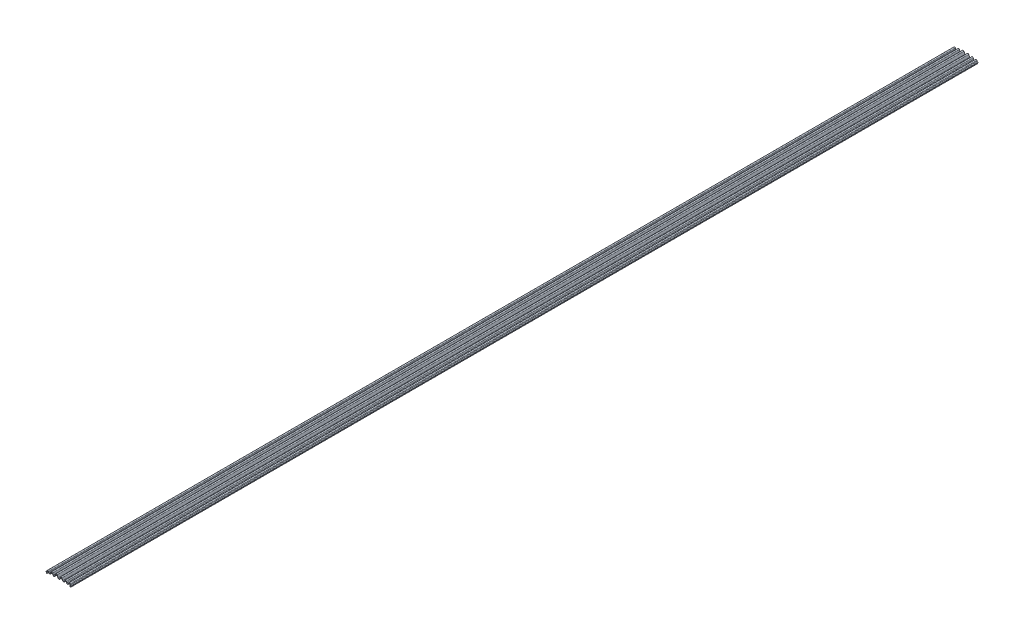
SolidWorks part; units mm, degrees
material "6463-T6"
ref_plane "Front Plane" through (0, 0, 0) normal (0, 0, 1) x (1, 0, 0)
ref_plane "Top Plane" through (0, 0, 0) normal (0, 1, 0) x (1, 0, 0)
ref_plane "Right Plane" through (0, 0, 0) normal (1, 0, 0) x (0, 0, -1)
sketch "Sketch1" plane through (0, 0, 0) normal (0, 0, 1) x (1, 0, 0)
  line L0 (-50.7848, 0.5715) -> (-50.5597, -0.0467)
  line L1 (-47.9908, -0.381) -> (-50.0824, -0.381)
  line L4 (-47.9908, -2.794) -> (-49.0157, -2.794)
  line L5 (-49.3737, -3.3053) -> (-49.1473, -3.9275)
  line L6 (-52.094, 1.3335) -> (52.094, 1.3335) construction
  line L7 (0, 14.1993) -> (0, -14.1993) construction
  line L9 (49.3737, -3.3053) -> (49.1473, -3.9275)
  line L10 (-50.7848, 1.3335) -> (-50.7848, 0.5715)
  line L12 (47.9908, -2.794) -> (49.0157, -2.794)
  line L14 (47.9908, -0.381) -> (50.0976, -0.381)
  line L15 (50.8, 0.5715) -> (50.575, -0.0467)
  line L20 (-46.5413, 2.5226) -> (-45.1353, 5.5376)
  line L21 (-41.6581, 5.5376) -> (-40.2522, 2.5226)
  line L22 (-31.7347, 2.5226) -> (-29.16, 8.0441)
  line L23 (-25.6828, 8.0441) -> (-23.1081, 2.5226)
  line L24 (-14.5906, 2.5226) -> (-10.6158, 11.0468)
  line L25 (-7.1385, 11.0468) -> (-3.1637, 2.5226)
  line L26 (5.3538, 2.5226) -> (8.8101, 9.9345)
  line L27 (12.2873, 9.9345) -> (15.7435, 2.5226)
  line L28 (24.261, 2.5226) -> (26.3257, 6.9503)
  line L29 (29.8029, 6.9503) -> (31.8675, 2.5226)
  line L30 (40.385, 2.5226) -> (41.6686, 5.2752)
  line L31 (45.1458, 5.2752) -> (46.382, 2.6241)
  line L33 (47.7632, 3.2681) -> (46.527, 5.9192)
  line L34 (40.2874, 5.9192) -> (39.0038, 3.1667)
  line L35 (33.2488, 3.1667) -> (31.1841, 7.5943)
  line L36 (24.9444, 7.5943) -> (22.8798, 3.1667)
  line L37 (17.1247, 3.1667) -> (13.6685, 10.5786)
  line L38 (7.4288, 10.5786) -> (3.9726, 3.1667)
  line L39 (-1.7824, 3.1667) -> (-5.7573, 11.6908)
  line L40 (-11.997, 11.6908) -> (-15.9719, 3.1667)
  line L41 (-21.7269, 3.1667) -> (-24.3016, 8.6881)
  line L42 (-30.5413, 8.6881) -> (-33.1159, 3.1667)
  line L43 (-38.871, 3.1667) -> (-40.2769, 6.1817)
  line L44 (-46.5226, 6.1686) -> (-47.9017, 3.1787)
  line L45 (50.8, 0.5715) -> (50.8, 1.3335)
  arc A0 (-47.9908, -2.794) -> (-47.9908, -0.381) centre (-47.9908, -1.5875) ccw
  arc A1 (-48.9187, -4.1555) -> (-46.9934, 0.9543) centre (-47.9908, -1.5875) ccw
  arc A2 (-48.9187, -4.1555) -> (-49.1473, -3.9275) centre (-48.7892, -3.7972) cw
  arc A3 (-49.0157, -2.794) -> (-49.3737, -3.3053) centre (-49.0157, -3.175) ccw
  arc A6 (49.0157, -2.794) -> (49.3737, -3.3053) centre (49.0157, -3.175) cw
  arc A7 (48.9187, -4.1555) -> (49.1473, -3.9275) centre (48.7892, -3.7972) ccw
  arc A8 (48.9187, -4.1555) -> (46.9391, 0.9324) centre (47.9908, -1.5875) cw
  arc A9 (47.9908, -2.794) -> (47.9908, -0.381) centre (47.9908, -1.5875) cw
  arc A12 (-47.1501, 1.5489) -> (-46.5413, 2.5226) centre (-50.8, 4.5085) ccw
  arc A13 (-41.6581, 5.5376) -> (-45.1353, 5.5376) centre (-43.3967, 4.7269) ccw
  arc A14 (-40.2522, 2.5226) -> (-31.7347, 2.5226) centre (-35.9935, 4.5085) ccw
  arc A15 (-25.6828, 8.0441) -> (-29.16, 8.0441) centre (-27.4214, 7.2333) ccw
  arc A16 (-23.1081, 2.5226) -> (-14.5906, 2.5226) centre (-18.8494, 4.5085) ccw
  arc A17 (-7.1385, 11.0468) -> (-10.6158, 11.0468) centre (-8.8771, 10.236) ccw
  arc A18 (-3.1637, 2.5226) -> (5.3538, 2.5226) centre (1.0951, 4.5085) ccw
  arc A19 (12.2873, 9.9345) -> (8.8101, 9.9345) centre (10.5487, 9.1238) ccw
  arc A20 (15.7435, 2.5226) -> (24.261, 2.5226) centre (20.0023, 4.5085) ccw
  arc A21 (29.8029, 6.9503) -> (26.3257, 6.9503) centre (28.0643, 6.1395) ccw
  arc A22 (31.8675, 2.5226) -> (40.385, 2.5226) centre (36.1263, 4.5085) ccw
  arc A23 (45.1458, 5.2752) -> (41.6686, 5.2752) centre (43.4072, 4.4644) ccw
  arc A24 (46.382, 2.6241) -> (47.0829, 1.5305) centre (50.8, 4.6842) ccw
  arc A25 (47.7632, 3.2681) -> (50.8, 1.3335) centre (50.8, 4.6842) ccw
  arc A26 (46.527, 5.9192) -> (40.2874, 5.9192) centre (43.4072, 4.4644) ccw
  arc A27 (33.2488, 3.1667) -> (39.0038, 3.1667) centre (36.1263, 4.5085) ccw
  arc A28 (31.1841, 7.5943) -> (24.9444, 7.5943) centre (28.0643, 6.1395) ccw
  arc A29 (17.1247, 3.1667) -> (22.8798, 3.1667) centre (20.0023, 4.5085) ccw
  arc A30 (13.6685, 10.5786) -> (7.4288, 10.5786) centre (10.5487, 9.1238) ccw
  arc A31 (-1.7824, 3.1667) -> (3.9726, 3.1667) centre (1.0951, 4.5085) ccw
  arc A32 (-5.7573, 11.6908) -> (-11.997, 11.6908) centre (-8.8771, 10.236) ccw
  arc A33 (-21.7269, 3.1667) -> (-15.9719, 3.1667) centre (-18.8494, 4.5085) ccw
  arc A34 (-24.3016, 8.6881) -> (-30.5413, 8.6881) centre (-27.4214, 7.2333) ccw
  arc A35 (-38.871, 3.1667) -> (-33.1159, 3.1667) centre (-35.9935, 4.5085) ccw
  arc A36 (-40.2769, 6.1817) -> (-46.5226, 6.1686) centre (-43.3967, 4.7269) ccw
  arc A37 (-50.7848, 1.3335) -> (-47.9017, 3.1787) centre (-50.7848, 4.5085) ccw
  arc A38 (-46.9934, 0.9543) -> (-47.1501, 1.5489) centre (-46.8542, 1.309) cw
  arc A39 (-50.0824, -0.381) -> (-50.5597, -0.0467) centre (-50.0824, 0.127) cw
  arc A40 (50.575, -0.0467) -> (50.0976, -0.381) centre (50.0976, 0.127) cw
  arc A41 (46.9391, 0.9324) -> (47.0829, 1.5305) centre (46.7924, 1.284) ccw
  point P2 (0, 1.3335)
  point P34 (49.5751, -3.3655)
  dimension "D1" = 2.413
  dimension "D2" = 5.461
  dimension "D4" = 0.381
  dimension "D5" = 3.175
  dimension "D9" = 0.508
  dimension "D12" = 0.508
  dimension "D14" = 104.188
  dimension "D11" = 0.381
  dimension "D17" = 0.381
  dimension "D3" = 50.7848
  dimension "D6" = 0.762
  dimension "D7" = 1.3335
  dimension "D8" = 0.762
  dimension "D10" = 20
  dimension "D13" = 2.794
  dimension "D15" = 1.3881
  dimension "D16" = 49.5751
  dimension "D18" = 3.3655
extrude "Boss-Extrude1" add sketch "Sketch1" against normal mid plane 3657.6
